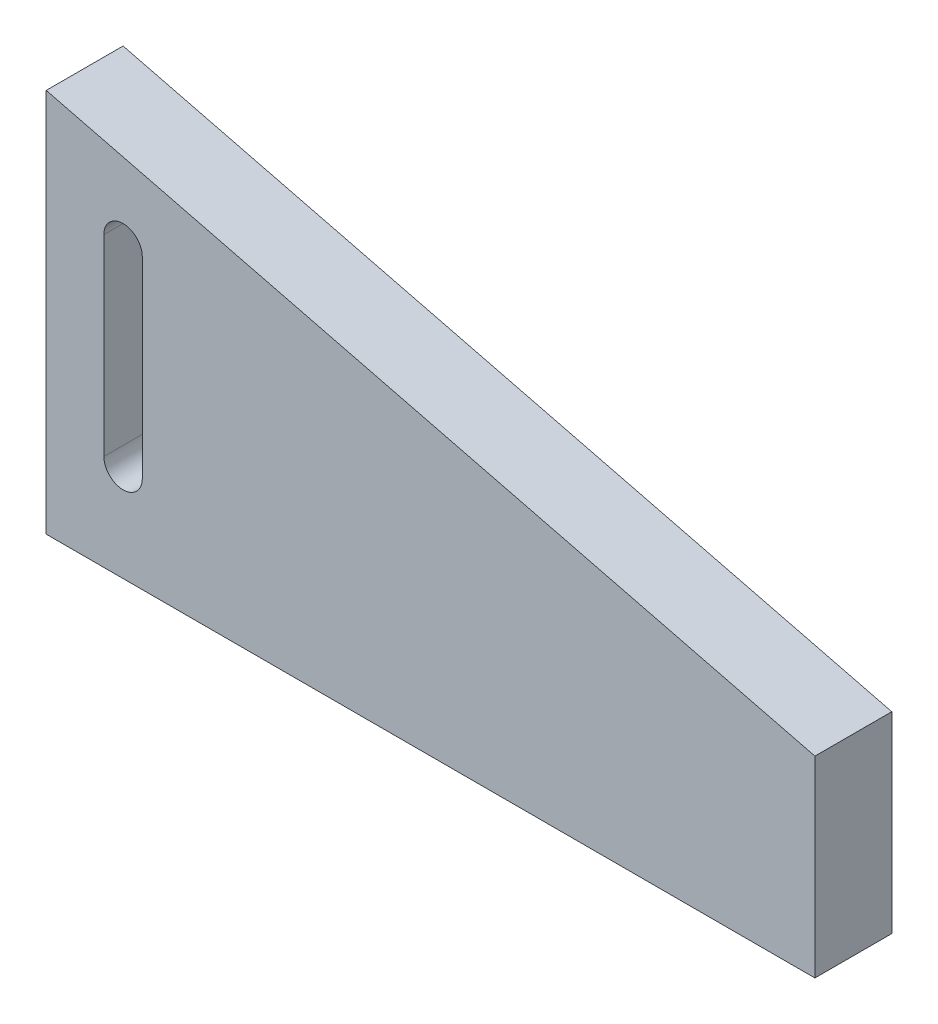
SolidWorks part; units mm, degrees
ref_plane "Ebene vorne" through (0, 0, 0) normal (0, 0, 1) x (1, 0, 0)
ref_plane "Ebene oben" through (0, 0, 0) normal (0, 1, 0) x (1, 0, 0)
ref_plane "Ebene rechts" through (0, 0, 0) normal (1, 0, 0) x (0, 0, -1)
sketch "Skizze1" plane through (0, 0, 0) normal (0, 0, 1) x (1, 0, 0)
  line L0 (0, 0) -> (0, 100)
  line L1 (0, 0) -> (200, 0)
  line L2 (200, 0) -> (200, 50)
  line L3 (200, 50) -> (0, 100)
  dimension "D1" = 100
  dimension "D2" = 200
  dimension "D3" = 50
extrude "Aufsatz-Linear austragen1" add sketch "Skizze1" along normal mid plane 20
sketch "Skizze2" plane through (0, 0, 10) normal (0, 0, 1) x (1, 0, 0)
  line L0 (0, 100) -> (0, 0) construction
  line L1 (20, 25) -> (20, 75) construction
  line L2 (15, 25) -> (15, 75)
  line L3 (0, 89.6922) -> (200, 39.6922) construction
  line L4 (200, 0) -> (200, 50) construction
  line L5 (200, 50) -> (0, 100) construction
  line L6 (0, 20) -> (200, 20) construction
  line L7 (25, 25) -> (25, 75)
  line L8 (0, 0) -> (200, 0) construction
  arc A0 (15, 25) -> (25, 25) centre (20, 25) ccw
  arc A1 (25, 75) -> (15, 75) centre (20, 75) ccw
  point P0 (0, 50)
  point P5 (20, 50)
  dimension "D1" = 20
  dimension "D2" = 50
  dimension "D3" = 10
  dimension "D4" = 10
  dimension "D5" = 20
extrude "Schnitt-Linear austragen1" cut sketch "Skizze2" against normal through all
pattern_linear "Lineares Muster1" count 6 spacing 15 along (0, 1, 0) of "Schnitt-Linear austragen1"
